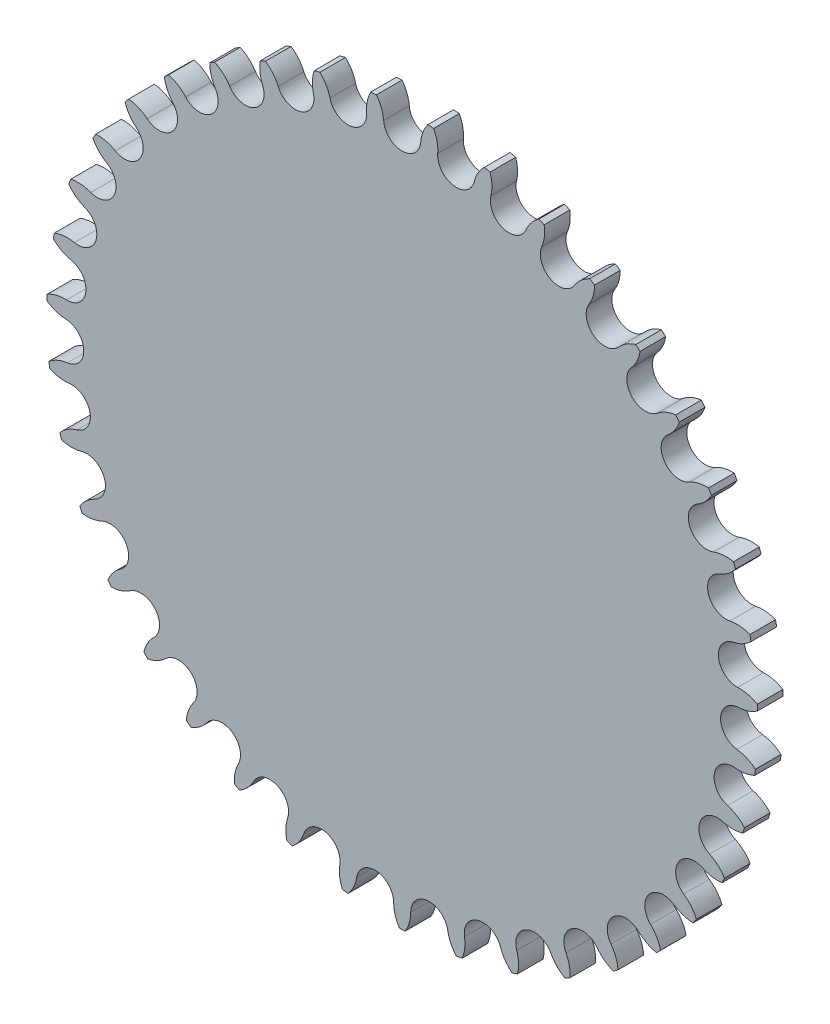
SolidWorks part; units mm, degrees
material "AISI 1020"
ref_plane "Спереди" through (0, 0, 0) normal (0, 0, 1) x (1, 0, 0)
ref_plane "Сверху" through (0, 0, 0) normal (0, 1, 0) x (1, 0, 0)
ref_plane "Справа" through (0, 0, 0) normal (1, 0, 0) x (0, 0, -1)
sketch "Эскиз1" plane through (0, 0, 0) normal (0, 0, 1) x (1, 0, 0)
  line L4 (0, 0) -> (0, 78.9148)
  line L5 (0, 78.9148) -> (12.6588, 77.8928)
  line L6 (12.6588, 77.8928) -> (0, 0)
  circle A1 centre (0, 78.9148) radius 4.255
  circle A2 centre (12.6588, 77.8928) radius 4.255
  circle A3 centre (0, 0) radius 83.1698 construction
  dimension "D6" = 8.51
  dimension "D1" = 166.3395
  dimension "D5" = 9.231
  dimension "D7" = 12.7
sketch "Эскиз2" plane through (0, 0, 0) normal (0, 0, 1) x (1, 0, 0)
  line L0 (0, 0) -> (0, 74.5598)
  line L1 (0, 0) -> (11.9602, 73.5942)
  line L4 (12.6588, 77.8928) -> (0, 0) construction
  arc A0 (8.3179, 78.2433) -> (7.3625, 82.8432) centre (0, 78.9148) ccw
  arc A1 (0, 83.1698) -> (13.3414, 82.0927) centre (0, 0) cw construction
  circle A2 centre (0, 78.9148) radius 4.255 construction
  circle A3 centre (12.6588, 77.8928) radius 4.255 construction
  circle A5 centre (0, 78.9148) radius 4.355
  arc A6 (0, 74.5598) -> (4.3409, 78.5643) centre (0, 78.9148) ccw
  arc A7 (6.0219, 82.9515) -> (4.3409, 78.5643) centre (12.6588, 77.8928) ccw
  circle A8 centre (12.6588, 77.8928) radius 4.355
  arc A9 (8.3179, 78.2433) -> (11.9602, 73.5942) centre (12.6588, 77.8928) ccw
  arc A10 (6.0219, 82.9515) -> (7.3625, 82.8432) centre (0, 0) cw
  dimension "D1" = 0.1
  dimension "D2" = 0.1
extrude "Бобышка-Вытянуть1" add sketch "Эскиз2" along normal blind 6
pattern_circular "Круговой массив1" count 39 over 360 about axis through (0, 0, 0) along (0, 0, 1) of "Бобышка-Вытянуть1"
sketch "Эскиз3" plane through (0, 0, 6) normal (0, 0, 1) x (1, 0, 0)
  line L0 (0, 0) -> (0, 30) construction
  line L1 (0, 0) -> (25.9808, 15) construction
  circle A0 centre (0, 0) radius 17.5
  circle A1 centre (0, 0) radius 30 construction
  circle A2 centre (0, 30) radius 4
  circle A3 centre (25.9808, 15) radius 4
  circle A4 centre (25.9808, -15) radius 4
  circle A5 centre (0, -30) radius 4
  circle A6 centre (-25.9808, -15) radius 4
  circle A7 centre (-25.9808, 15) radius 4
  dimension "D1" = 35
  dimension "D2" = 60
  dimension "D3" = 8
  dimension "D5" = 60
  dimension "D6" = 30
  dimension "D4" = 6
extrude "Вырез-Вытянуть1" [suppressed] cut sketch "Эскиз3" against normal through all
equation "\"D5@Эскиз1\"=360/\"_kol-vo\""
equation "\"_kol-vo\" = 39"
equation "\"_Pitch\"=12.7"
equation "\"_d1_max\"= 8.51"
equation "\"_d1_min\"= 7.75"
equation "\"_d2_max\"= 4.45"
equation "\"_T_max\"= 1.6"
equation "\"_h2\"= 11.8"
equation "\"_L_max\"= 16.85"
equation "\"_Lc_max\"= 18.1"
equation "\"D6@Эскиз1\"=\"_d1_max\""
equation "\"D1@Круговой массив1\"=\"_kol-vo\""
equation "\"D7@Эскиз1\"=\"_Pitch\""
